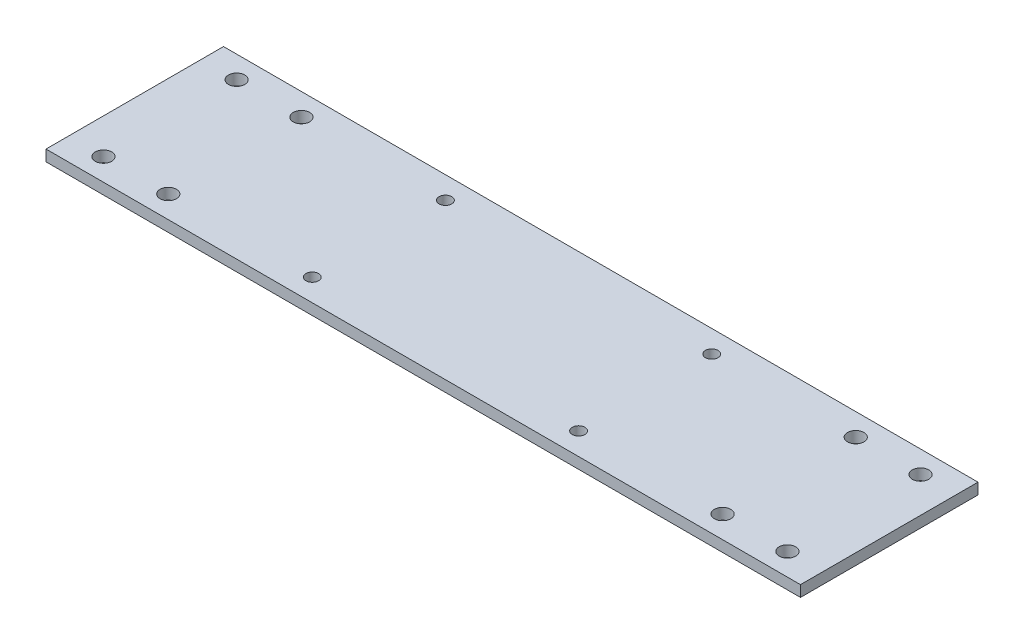
SolidWorks part; units mm, degrees
ref_plane "Front Plane" through (0, 0, 0) normal (0, 0, 1) x (1, 0, 0)
ref_plane "Top Plane" through (0, 0, 0) normal (0, 1, 0) x (1, 0, 0)
ref_plane "Right Plane" through (0, 0, 0) normal (1, 0, 0) x (0, 0, -1)
sketch "Sketch1" plane through (0, 0, 0) normal (0, 1, 0) x (1, 0, 0)
  line L1 (-107.95, -25.4) -> (107.95, -25.4)
  line L2 (-107.95, -25.4) -> (-107.95, 25.4)
  line L3 (-107.95, 25.4) -> (107.95, 25.4)
  line L4 (107.95, -25.4) -> (107.95, 25.4)
  line L5 (-107.95, -25.4) -> (107.95, 25.4) construction
  line L6 (-107.95, 25.4) -> (107.95, -25.4) construction
  line L7 (38.1, -19.05) -> (-38.1, -19.05) construction
  line L8 (38.1, -19.05) -> (38.1, 19.05) construction
  line L9 (38.1, 19.05) -> (-38.1, 19.05) construction
  line L10 (-38.1, -19.05) -> (-38.1, 19.05) construction
  line L11 (38.1, -19.05) -> (-38.1, 19.05) construction
  line L12 (38.1, 19.05) -> (-38.1, -19.05) construction
  circle A0 centre (-38.1, 19.05) radius 1.8097
  circle A1 centre (-38.1, -19.05) radius 1.8097
  circle A2 centre (38.1, 19.05) radius 1.8097
  circle A3 centre (38.1, -19.05) radius 1.8097
  point P0 (0, 0)
  point P14 (0, 0)
  dimension "D3" = 3.6195
  dimension "D4" = 38.1
  dimension "D1" = 215.9
  dimension "D2" = 50.8
  dimension "D5" = 76.2
extrude "Boss-Extrude1" add sketch "Sketch1" along normal blind 3.175
sketch "Sketch2" plane through (0, 3.175, 0) normal (0, 1, 0) x (1, 0, 0)
  line L0 (-97.8535, 19.05) -> (-107.95, 19.05) construction
  line L1 (-107.95, 25.4) -> (-107.95, -25.4) construction
  line L3 (107.95, 25.4) -> (-107.95, 25.4) construction
  line L4 (0, 25.4) -> (0, -25.4) construction
  line L6 (-107.95, -25.4) -> (107.95, -25.4) construction
  line L7 (97.8535, -19.05) -> (97.8535, -25.4) construction
  line L8 (97.8535, 22.86) -> (97.8535, 19.05) construction
  line L9 (97.8535, 19.05) -> (107.95, 19.05) construction
  line L10 (-97.8535, 25.4) -> (-97.8535, 21.3995) construction
  line L12 (-97.8535, -21.3995) -> (-97.8535, -25.4) construction
  circle A0 centre (-97.8535, 19.05) radius 2.3495
  circle A1 centre (-79.3115, 19.05) radius 2.3495
  circle A2 centre (-79.3115, -19.05) radius 2.3495
  circle A3 centre (-97.8535, -19.05) radius 2.3495
  circle A4 centre (97.8535, -19.05) radius 2.3495
  circle A5 centre (79.3115, -19.05) radius 2.3495
  circle A6 centre (79.3115, 19.05) radius 2.3495
  circle A7 centre (97.8535, 19.05) radius 2.3495
  dimension "D4" = 4.699
  dimension "D1" = 18.542
  dimension "D2" = 10.0965
  dimension "D3" = 4.0005
extrude "Cut-Extrude1" cut sketch "Sketch2" against normal through all
